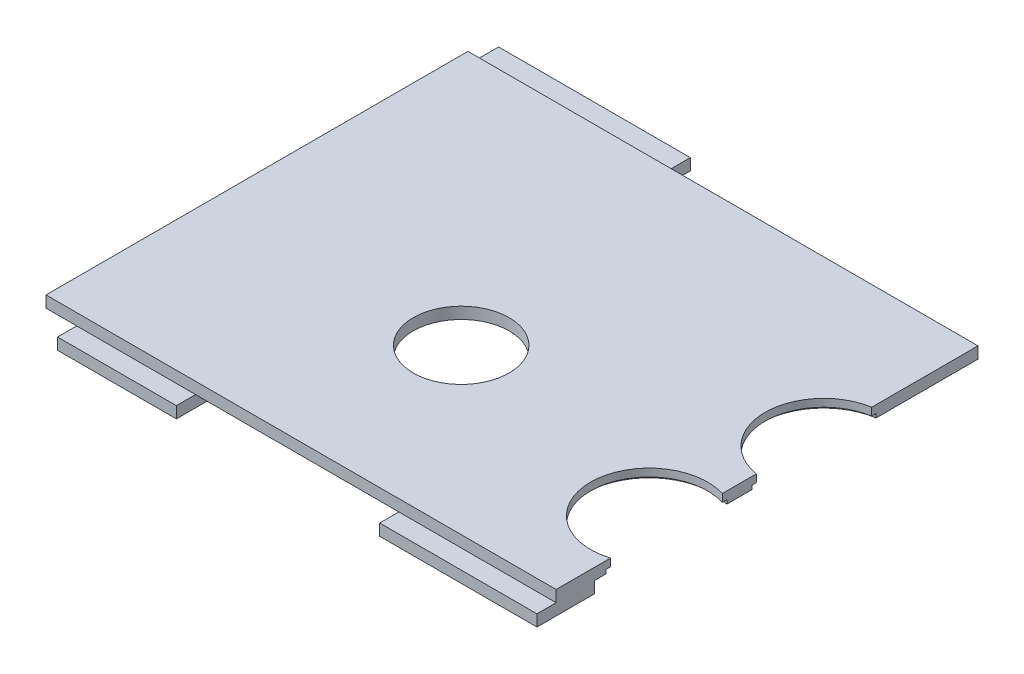
SolidWorks part; units mm, degrees
ref_plane "Front Plane" through (0, 0, 0) normal (0, 0, 1) x (1, 0, 0)
ref_plane "Top Plane" through (0, 0, 0) normal (0, 1, 0) x (1, 0, 0)
ref_plane "Right Plane" through (0, 0, 0) normal (1, 0, 0) x (0, 0, -1)
sketch "Sketch1" plane through (0, 0, 0) normal (0, 1, 0) x (1, 0, 0)
  line L1 (0, 0) -> (133, 0)
  line L2 (0, 0) -> (0, 110)
  line L3 (0, 110) -> (133, 110)
  line L4 (133, 0) -> (133, 110)
  dimension "D1" = 110
  dimension "D2" = 133
extrude "Boss-Extrude1" add sketch "Sketch1" along normal blind 3
sketch "Sketch2" plane through (0, 0, 0) normal (0, -1, 0) x (1, 0, 0)
  line L0 (133, 0) -> (133, -110) construction
  line L1 (0, -118) -> (50, -118)
  line L2 (0, -118) -> (0, -100)
  line L3 (0, -100) -> (50, -100)
  line L4 (50, -118) -> (50, -100)
  line L5 (133, -110) -> (0, -110) construction
  line L6 (133, -10) -> (92, -10)
  line L7 (133, -10) -> (133, 5)
  line L8 (133, 5) -> (92, 5)
  line L9 (8, -10) -> (8, 5)
  line L10 (0, -110) -> (0, 0) construction
  line L11 (0, 0) -> (133, 0) construction
  line L12 (39, -10) -> (39, 5)
  line L13 (92, -10) -> (92, 5)
  line L14 (0, -110) -> (0, 0) construction
  line L15 (39, -10) -> (8, -10)
  line L16 (39, 5) -> (8, 5)
  point P22 (133, -2.5)
  dimension "D1" = 10
  dimension "D2" = 18
  dimension "D3" = 50
  dimension "D4" = 15
  dimension "D5" = 10
  dimension "D6" = 8
  dimension "D7" = 39
  dimension "D8" = 41
extrude "Boss-Extrude2" add sketch "Sketch2" along normal blind 3
sketch "Sketch3" plane through (0, 3, 0) normal (0, 1, 0) x (1, 0, 0)
  line L0 (133, 110) -> (0, 110) construction
  line L1 (0, 110) -> (0, 0) construction
  circle A0 centre (65.5, 42.75) radius 12.5
  circle A1 centre (128.5, 28.75) radius 15.25
  circle A2 centre (135.5, 67.25) radius 15.25
  dimension "D1" = 25
  dimension "D4" = 30.5
  dimension "D5" = 63
  dimension "D2" = 67.25
  dimension "D3" = 65.5
  dimension "D6" = 14
  dimension "D7" = 70
  dimension "D8" = 24.5
extrude "Cut-Extrude1" cut sketch "Sketch3" against normal up to next
sketch "Sketch4" plane through (0, 0, 0) normal (0, -1, 0) x (1, 0, 0)
  circle A0 centre (128.5, -28.75) radius 16.375
  circle A1 centre (135.5, -67.25) radius 16.375
  dimension "D1" = 32.75
extrude "Cut-Extrude2" cut sketch "Sketch4" against normal blind 1
